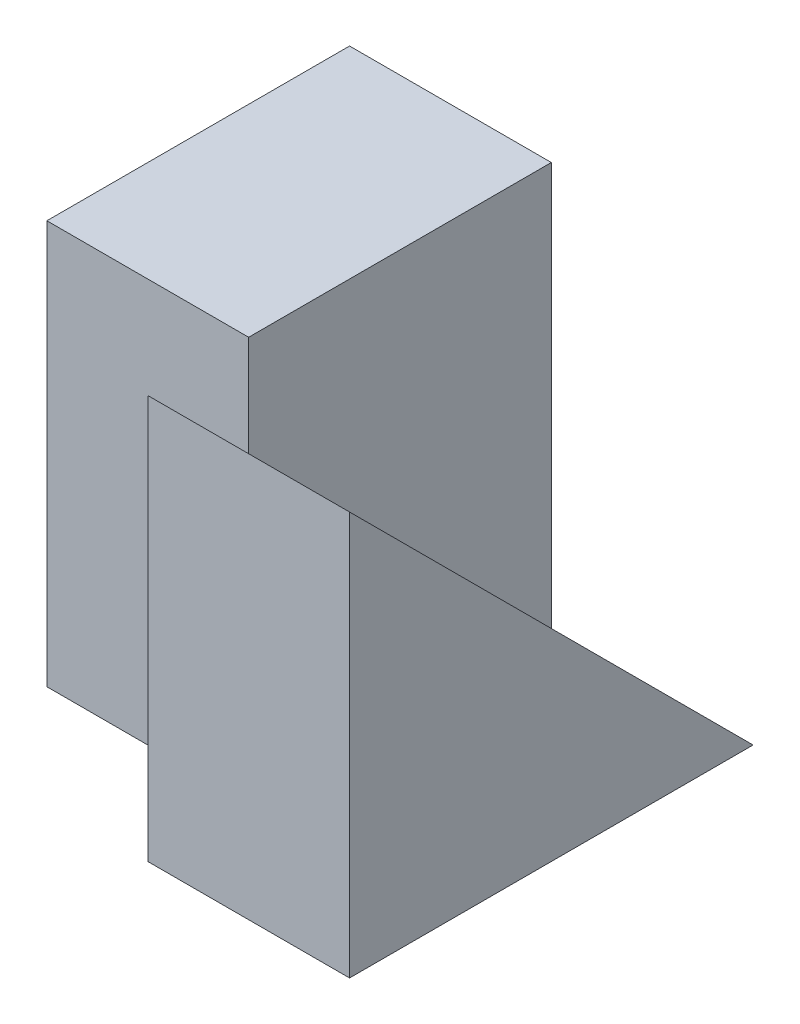
SolidWorks part; units mm, degrees
ref_plane "Front Plane" through (0, 0, 0) normal (0, 0, 1) x (1, 0, 0)
ref_plane "Top Plane" through (0, 0, 0) normal (0, 1, 0) x (1, 0, 0)
ref_plane "Right Plane" through (0, 0, 0) normal (1, 0, 0) x (0, 0, -1)
sketch "Sketch1" plane through (0, 0, 0) normal (1, 0, 0) x (0, 0, -1)
  line L1 (0, 0) -> (4, 0)
  line L2 (0, 0) -> (0, 4)
  line L3 (0, 4) -> (4, 4)
  line L4 (4, 0) -> (4, 4)
  dimension "D1" = 4
  dimension "D2" = 4
extrude "Boss-Extrude1" add sketch "Sketch1" along normal blind 2
sketch "Sketch2" plane through (0, 0, 0) normal (-1, 0, 0) x (0, 0, 1)
  line L0 (-1, 0) -> (-1, 4)
  line L1 (0, 0) -> (-4, 0) construction
  line L2 (-4, 0) -> (-4, 4) construction
  line L3 (-4, 4) -> (-4, 0)
  line L4 (-4, 0) -> (-1, 0)
  line L5 (-4, 4) -> (0, 4) construction
  line L6 (-1, 4) -> (-4, 4)
  dimension "D1" = 3
  dimension "D2" = 4
extrude "Boss-Extrude2" add sketch "Sketch2" along normal blind 2
sketch "Sketch3" plane through (2, 0, 0) normal (1, 0, 0) x (0, 0, -1)
  line L0 (4, 0) -> (0, 4)
  line L1 (0, 4) -> (0, 0) construction
  line L2 (0, 4) -> (4, 4)
  line L3 (4, 4) -> (4, 0)
extrude "Cut-Extrude1" cut sketch "Sketch3" against normal blind 2
